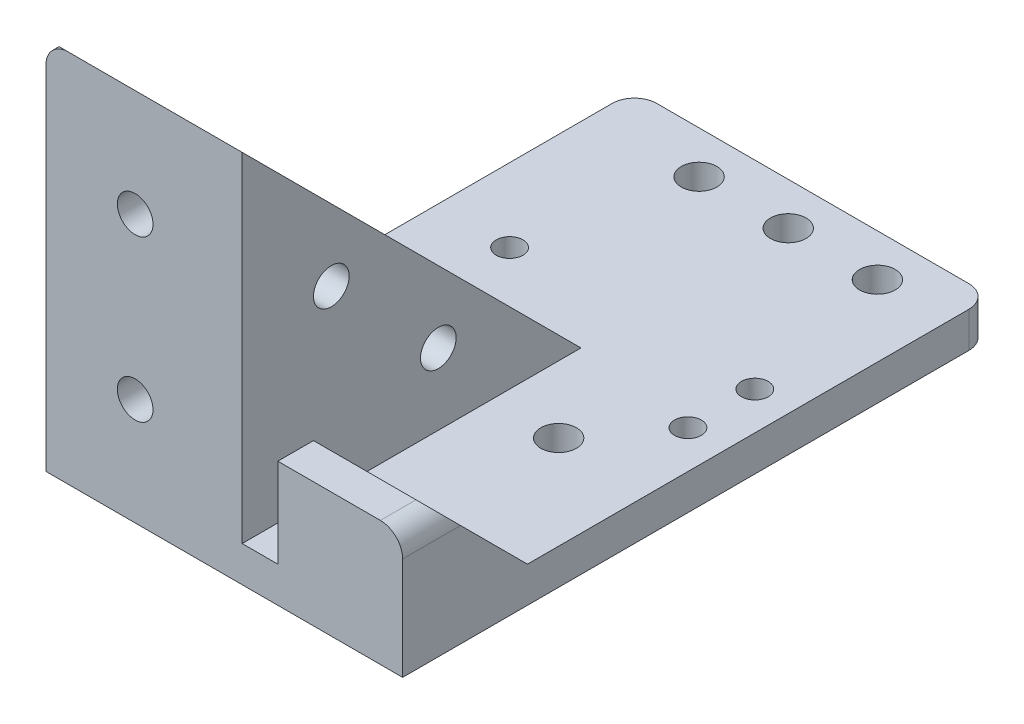
SolidWorks part; units mm, degrees
ref_plane "Front Plane" through (0, 0, 0) normal (0, 0, 1) x (1, 0, 0)
ref_plane "Top Plane" through (0, 0, 0) normal (0, 1, 0) x (1, 0, 0)
ref_plane "Right Plane" through (0, 0, 0) normal (1, 0, 0) x (0, 0, -1)
sketch "Sketch1" plane through (0, 0, 0) normal (0, 1, 0) x (1, 0, 0)
  line L0 (0, 108.3742) -> (0, -10.7395) construction
  line L1 (-51.4374, 0) -> (47.9292, 0) construction
  line L6 (-20, 66) -> (20, 66)
  line L7 (-20, 66) -> (-20, 6)
  line L9 (20, 66) -> (20, 6)
  line L10 (-20, 66) -> (20, 6) construction
  line L11 (-20, 6) -> (20, 66) construction
  line L12 (-20, 0) -> (20, 0)
  line L16 (-20, 6) -> (-20, 0)
  line L17 (20, 6) -> (20, 0)
  line L19 (-19.5962, 6) -> (43.0349, 6) construction
  point P3 (0, 36)
  dimension "D1" = 40
  dimension "D2" = 60
  dimension "D3" = 6
extrude "Boss-Extrude1" add sketch "Sketch1" along normal blind 4
sketch "Sketch2" plane through (0, 4, 0) normal (0, 1, 0) x (1, 0, 0)
  line L0 (-8.0039, 61.25) -> (11.9961, 61.25) construction
  line L1 (1.9961, -14.7291) -> (1.9961, 58.7438) construction
  line L2 (-11.7539, 43.75) -> (15.7461, 43.75) construction
  line L3 (-11.7539, 43.75) -> (-11.7539, 36.25) construction
  line L4 (-11.7539, 36.25) -> (15.7461, 36.25) construction
  line L5 (15.7461, 43.75) -> (15.7461, 36.25) construction
  line L6 (-11.7539, 43.75) -> (15.7461, 36.25) construction
  line L7 (-11.7539, 36.25) -> (15.7461, 43.75) construction
  line L8 (-5.5039, 8) -> (9.4961, 8) construction
  line L9 (-5.5039, 8) -> (-5.5039, 28) construction
  line L10 (-5.5039, 28) -> (9.4961, 28) construction
  line L11 (9.4961, 8) -> (9.4961, 28) construction
  line L12 (-5.5039, 8) -> (9.4961, 28) construction
  line L13 (-5.5039, 28) -> (9.4961, 8) construction
  line L16 (20, 66) -> (-20, 66) construction
  circle A0 centre (-8.0039, 61.25) radius 2
  circle A1 centre (1.9961, 61.25) radius 2
  circle A2 centre (11.9961, 61.25) radius 2
  circle A3 centre (-5.5039, 8) radius 2
  circle A4 centre (-5.5039, 28) radius 2
  circle A5 centre (9.4961, 28) radius 2
  circle A6 centre (9.4961, 8) radius 2
  circle A7 centre (15.7461, 36.25) radius 1.5
  circle A8 centre (15.7461, 43.75) radius 1.5
  circle A9 centre (-11.7539, 43.75) radius 1.5
  circle A10 centre (-11.7539, 36.25) radius 1.5
  point P2 (1.9961, 40)
  point P12 (1.9961, 18)
  point P20 (1.9961, 61.25)
  dimension "D10" = 4
  dimension "D11" = 4
  dimension "D12" = 3
  dimension "D1" = 20
  dimension "D2" = 15
  dimension "D3" = 48
  dimension "D4" = 7.5
  dimension "D5" = 27.5
  dimension "D6" = 26
  dimension "D7" = 4.75
  dimension "D8" = 20
  dimension "D9" = 10
  dimension "D13" = 1.9961
extrude "Cut-Extrude1" cut sketch "Sketch2" against normal through all
ref_plane "Plane1" through (2, 0, 0) normal (1, 0, 0) x (0, 0, -1)
sketch "Sketch5" plane through (2, 0, 0) normal (1, 0, 0) x (0, 0, -1)
  line L0 (0, 4) -> (0, 38)
  line L1 (0, 38) -> (4, 38)
  line L2 (4, 38) -> (38, 4)
  line L4 (0, 4) -> (66, 4) construction
  line L5 (38, 4) -> (0, 4)
  point P4 (41.3463, 4)
  point P10 (38.0264, 4)
  point P11 (38.0849, 4)
  dimension "D1" = 34
  dimension "D2" = 4
  dimension "D4" = 45
extrude "Boss-Extrude5" add sketch "Sketch5" against normal blind 4
sketch "Sketch6" plane through (0, 0, 0) normal (0, 0, 1) x (1, 0, 0)
  line L0 (-2, 38) -> (-20, 38)
  line L1 (-2, 38) -> (2, 38) construction
  line L2 (-2, 38) -> (-2, 4) construction
  line L3 (-20, 38) -> (-20, 4)
  line L4 (-20, 4) -> (-2, 4)
  line L5 (-2, 4) -> (-2, 38)
extrude "Boss-Extrude6" add sketch "Sketch6" against normal blind 4
sketch "Sketch7" plane through (0, 0, 0) normal (0, 0, 1) x (1, 0, 0)
  line L0 (6, 4) -> (6, 14)
  line L1 (2, 4) -> (20, 4) construction
  line L2 (6, 14) -> (20, 14)
  line L4 (2, 38) -> (2, 4) construction
  line L5 (6, 4) -> (20, 4)
  line L6 (20, 4) -> (20, 0) construction
  line L7 (20, 4) -> (20, 14)
  dimension "D1" = 4
  dimension "D2" = 10
extrude "Boss-Extrude7" add sketch "Sketch7" against normal blind 4
sketch "Sketch8" plane through (-2, 0, 0) normal (-1, 0, 0) x (0, 0, 1)
  line L0 (-32, 12) -> (-10, 12) construction
  line L1 (-10, 32) -> (-10, 12) construction
  line L2 (-4, 4) -> (-38, 4) construction
  line L3 (0, 38) -> (0, 0) construction
  circle A1 centre (-10, 24) radius 2
  circle A2 centre (-22, 12) radius 2
  dimension "D3" = 4
  dimension "D1" = 12
  dimension "D2" = 12
  dimension "D4" = 10
  dimension "D5" = 8
  dimension "D6" = 10
extrude "Cut-Extrude2" cut sketch "Sketch8" against normal through all
sketch "Sketch9" plane through (0, 0, -4) normal (0, 0, -1) x (-1, 0, 0)
  line L0 (10, 4.695) -> (10, 30.9324) construction
  line L1 (20, 38) -> (20, 4) construction
  line L2 (-20, 4) -> (20, 4) construction
  circle A0 centre (10, 12) radius 2
  circle A1 centre (10, 30) radius 2
  dimension "D4" = 4
  dimension "D1" = 10
  dimension "D2" = 18
  dimension "D3" = 8
extrude "Cut-Extrude3" cut sketch "Sketch9" against normal blind 4
fillet "Fillet1" [suppressed] radius 4
sketch "Sketch10" plane through (2, 0, 0) normal (1, 0, 0) x (0, 0, -1)
  line L0 (4, 38) -> (0, 42)
  line L1 (0, 42) -> (0, 38)
  line L2 (0, 38) -> (4, 38)
extrude "Boss-Extrude8" add sketch "Sketch10" against normal up to surface (22 mm away) up to face at (-20, 14, -23.3333)
sketch "Sketch13" plane through (20, 0, 0) normal (1, 0, 0) x (0, 0, -1)
  line L0 (4, 14) -> (14, 4)
  line L1 (4, 4) -> (4, 14) construction
  line L2 (4, 4) -> (66, 4) construction
  line L3 (4, 14) -> (4, 4)
  line L4 (4, 4) -> (14, 4)
  line L5 (4, 14) -> (0, 14) construction
  dimension "D1" = 45
extrude "Boss-Extrude9" add sketch "Sketch13" against normal blind 4
sketch "Sketch14" plane through (-20, 0, 0) normal (-1, 0, 0) x (0, 0, 1)
  line L0 (-4, 38) -> (-38, 4)
  line L3 (-38, 4) -> (-4, 4)
  line L4 (-4, 4) -> (-4, 38)
  line L5 (-66, 4) -> (-4, 4) construction
  point P1 (-40.4906, 4)
  point P4 (-38.0133, 4)
  point P5 (-4, 38)
  point P6 (-37.7346, 4)
  dimension "D1" = 45
extrude "Boss-Extrude10" add sketch "Sketch14" against normal blind 4
sketch "Sketch16" plane through (0, 0, 0) normal (0, 0, 1) x (1, 0, 0)
  line L0 (-20, 42) -> (-20, 0) construction
  line L1 (-20, 42) -> (2, 42) construction
  line L2 (-20, 39.5668) -> (-20, 42)
  line L3 (-20, 42) -> (-17.4086, 42)
  arc A0 (-20, 39.5668) -> (-17.4086, 42) centre (-17.5008, 39.5017) cw
  line M5 (-20, 42) -> (-20, 0)
  dimension "D1" = 2.5
extrude "Cut-Extrude5" cut sketch "Sketch16" against normal blind 4 contours A0 L3 M5
fillet "Fillet7" radius 2.5 2 edges at (-20, 2, -66) (20, 2, -66)
fillet "Fillet8" radius 2.5 1 edges at (20, 14, -2)
